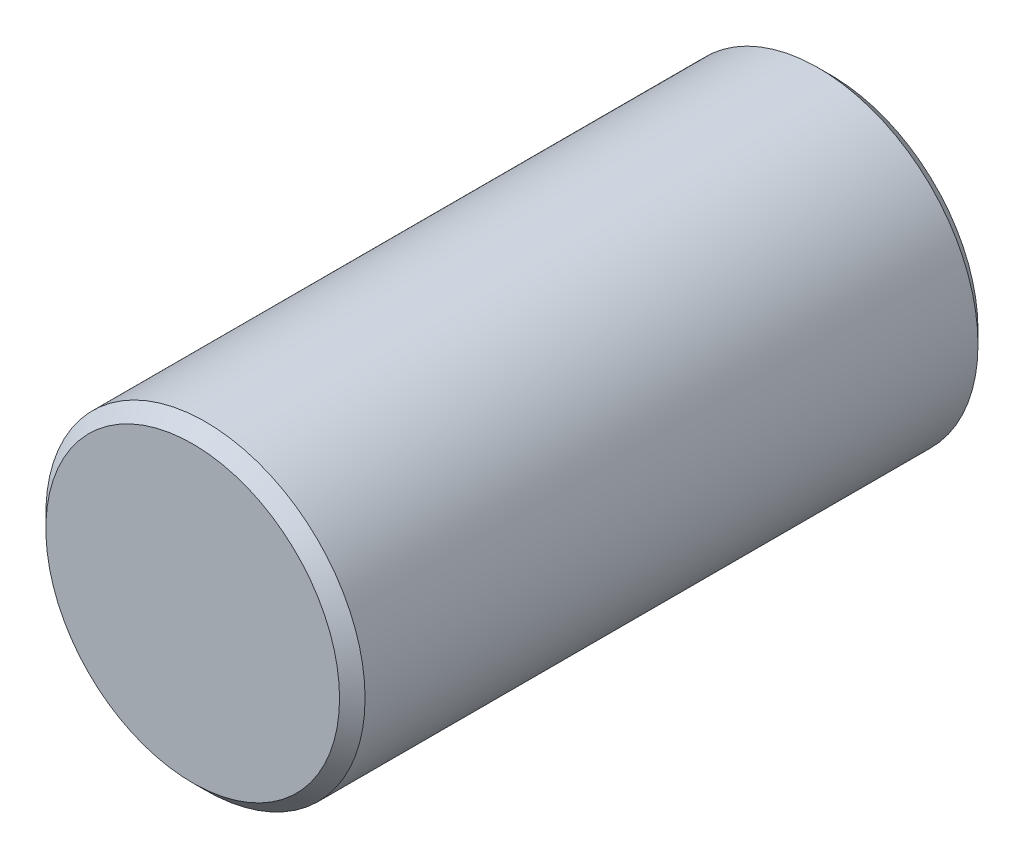
SolidWorks part; units mm, degrees
material "Copper"
ref_plane "Front Plane" through (0, 0, 0) normal (0, 0, 1) x (1, 0, 0)
ref_plane "Top Plane" through (0, 0, 0) normal (0, 1, 0) x (1, 0, 0)
ref_plane "Right Plane" through (0, 0, 0) normal (1, 0, 0) x (0, 0, -1)
sketch "Sketch1" plane through (0, 0, 0) normal (0, 0, 1) x (1, 0, 0)
  circle A0 centre (0, 0) radius 1.25
  dimension "D1" = 2.5
extrude "Boss-Extrude1" add sketch "Sketch1" along normal blind 5
chamfer "Chamfer1" distance 0.1 angle 45 2 edges at (1.25, 0, 0) (1.25, 0, 5)
